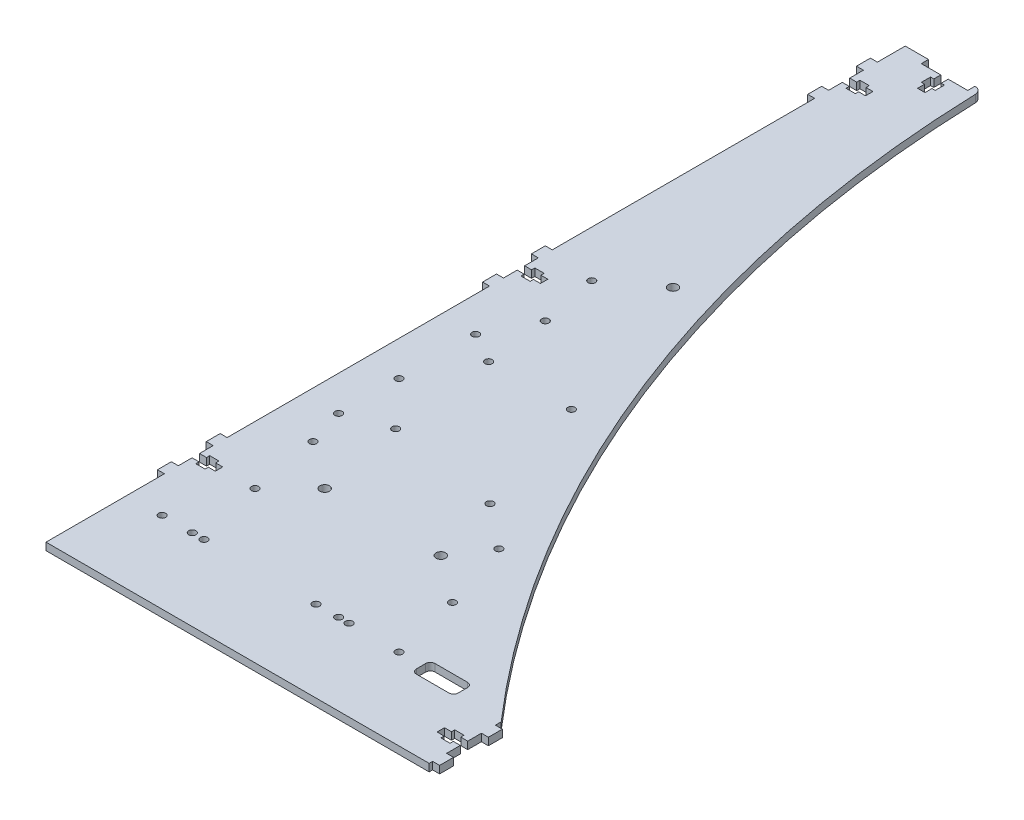
SolidWorks part; units mm, degrees
ref_plane "Alzado" through (0, 0, 0) normal (0, 0, 1) x (1, 0, 0)
ref_plane "Planta" through (0, 0, 0) normal (0, 1, 0) x (1, 0, 0)
ref_plane "Vista lateral" through (0, 0, 0) normal (1, 0, 0) x (0, 0, -1)
sketch "Croquis1" plane through (0, 0, 0) normal (0, 1, 0) x (1, 0, 0)
  line L0 (7, 66.1) -> (10, 66.1)
  line L1 (0, 0) -> (165, 0)
  line L2 (0, 0) -> (0, 51)
  line L3 (0, 370) -> (10, 370)
  line L4 (165, 0) -> (165, 1.5)
  line L5 (0, 51) -> (-3, 51)
  line L7 (0, 57) -> (-3, 57)
  line L8 (-3, 51) -> (-3, 57)
  line L9 (0, 72) -> (-3, 72)
  line L11 (0, 78) -> (-3, 78)
  line L12 (-3, 72) -> (-3, 78)
  line L13 (0, 66.1) -> (3, 66.1)
  line L15 (0, 62.9) -> (3, 62.9)
  line L16 (10, 66.1) -> (10, 62.9)
  line L17 (7, 67.5) -> (3, 67.5)
  line L18 (7, 67.5) -> (7, 66.1)
  line L19 (7, 61.5) -> (3, 61.5)
  line L20 (3, 67.5) -> (3, 66.1)
  line L21 (3, 62.9) -> (3, 61.5)
  line L22 (7, 62.9) -> (7, 61.5)
  line L23 (7, 62.9) -> (10, 62.9)
  line L24 (0, 66.1) -> (0, 72)
  line L25 (0, 78) -> (0, 191)
  line L26 (0, 57) -> (0, 62.9)
  line L27 (0, 218) -> (-3, 218)
  line L28 (-3, 212) -> (-3, 218)
  line L29 (0, 212) -> (-3, 212)
  line L30 (0, 206.1) -> (3, 206.1)
  line L31 (3, 207.5) -> (3, 206.1)
  line L32 (7, 207.5) -> (3, 207.5)
  line L33 (7, 207.5) -> (7, 206.1)
  line L34 (7, 206.1) -> (10, 206.1)
  line L35 (10, 206.1) -> (10, 202.9)
  line L36 (7, 202.9) -> (10, 202.9)
  line L37 (7, 202.9) -> (7, 201.5)
  line L38 (7, 201.5) -> (3, 201.5)
  line L39 (3, 202.9) -> (3, 201.5)
  line L40 (0, 202.9) -> (3, 202.9)
  line L41 (0, 197) -> (-3, 197)
  line L42 (-3, 191) -> (-3, 197)
  line L43 (0, 191) -> (-3, 191)
  line L44 (0, 358) -> (-3, 358)
  line L45 (-3, 352) -> (-3, 358)
  line L46 (0, 352) -> (-3, 352)
  line L47 (0, 346.1) -> (3, 346.1)
  line L48 (3, 347.5) -> (3, 346.1)
  line L49 (7, 347.5) -> (3, 347.5)
  line L50 (7, 347.5) -> (7, 346.1)
  line L51 (7, 346.1) -> (10, 346.1)
  line L52 (10, 346.1) -> (10, 342.9)
  line L53 (7, 342.9) -> (10, 342.9)
  line L54 (7, 342.9) -> (7, 341.5)
  line L55 (7, 341.5) -> (3, 341.5)
  line L56 (3, 342.9) -> (3, 341.5)
  line L57 (0, 342.9) -> (3, 342.9)
  line L58 (0, 337) -> (-3, 337)
  line L59 (-3, 331) -> (-3, 337)
  line L60 (0, 331) -> (-3, 331)
  line L61 (0, 358) -> (0, 370)
  line L62 (0, 346.1) -> (0, 352)
  line L63 (0, 337) -> (0, 342.9)
  line L64 (0, 218) -> (0, 331)
  line L65 (0, 206.1) -> (0, 212)
  line L66 (0, 197) -> (0, 202.9)
  line L67 (21.6, 366.9) -> (30, 366.9)
  line L69 (10, 370) -> (10, 366.9)
  line L70 (10, 366.9) -> (18.4, 366.9)
  line L71 (30, 370) -> (30, 366.9)
  line L73 (18.4, 366.9) -> (18.4, 363.9)
  line L74 (18.4, 356.9) -> (21.6, 356.9)
  line L75 (21.6, 366.9) -> (21.6, 363.9)
  line L76 (17, 363.9) -> (18.4, 363.9)
  line L77 (17, 363.9) -> (17, 359.9)
  line L78 (17, 359.9) -> (18.4, 359.9)
  line L79 (23, 363.9) -> (23, 359.9)
  line L80 (21.6, 363.9) -> (23, 363.9)
  line L81 (18.4, 359.9) -> (18.4, 356.9)
  line L82 (21.6, 359.9) -> (21.6, 356.9)
  line L83 (21.6, 359.9) -> (23, 359.9)
  line L84 (30, 370) -> (165, 370)
  line L85 (158, 13.4) -> (158, 12)
  line L86 (165, 1.5) -> (168, 1.5)
  line L88 (165, 7.5) -> (168, 7.5)
  line L89 (168, 1.5) -> (168, 7.5)
  line L90 (165, 22.5) -> (168, 22.5)
  line L92 (165, 28.5) -> (168, 28.5)
  line L93 (168, 22.5) -> (168, 28.5)
  line L94 (165, 16.6) -> (162, 16.6)
  line L96 (165, 13.4) -> (162, 13.4)
  line L97 (155, 16.6) -> (155, 13.4)
  line L98 (158, 18) -> (162, 18)
  line L99 (158, 18) -> (158, 16.6)
  line L100 (158, 12) -> (162, 12)
  line L101 (162, 18) -> (162, 16.6)
  line L102 (158, 16.6) -> (155, 16.6)
  line L103 (162, 13.4) -> (162, 12)
  line L104 (158, 13.4) -> (155, 13.4)
  line L105 (165, 16.6) -> (165, 22.5)
  line L106 (165, 7.5) -> (165, 13.4)
  line L107 (165, 28.5) -> (165, 370)
  dimension "D1" = 370
  dimension "D2" = 165
  dimension "D3" = 3
  dimension "D4" = 6
  dimension "D5" = 3
  dimension "D6" = 6
  dimension "D7" = 15
  dimension "D8" = 10
  dimension "D9" = 3.2
  dimension "D10" = 5.9
  dimension "D11" = 4
  dimension "D12" = 6
  dimension "D13" = 1.4
  dimension "D14" = 51
  dimension "D15" = 3
  dimension "D17" = 140
  dimension "D18" = 20
  dimension "D19" = 10
  dimension "D20" = 3.1
  dimension "D21" = 10
  dimension "D22" = 3.2
  dimension "D23" = 4
  dimension "D24" = 6
  dimension "D25" = 1.4
  dimension "D26" = 8.4
  dimension "D27" = 3
  dimension "D28" = 6
  dimension "D29" = 6
  dimension "D30" = 3
  dimension "D31" = 3
  dimension "D32" = 3.2
  dimension "D33" = 4
  dimension "D34" = 6
  dimension "D35" = 1.4
  dimension "D36" = 10
  dimension "D37" = 3
  dimension "D38" = 15
  dimension "D39" = 5.9
  dimension "D40" = 1.5
  dimension "D16" = 3
extrude "Saliente-Extruir1" add sketch "Croquis1" along normal blind 3.2
sketch "Croquis2" plane through (0, 0, 0) normal (0, -1, 0) x (1, 0, 0)
  line L0 (30, -370) -> (30, -366.9) construction
  line L1 (165, -370) -> (33, -370)
  line L2 (165, -370) -> (165, -31)
  line L3 (165, -31) -> (33, -31) construction
  line L4 (33, -370) -> (33, -31) construction
  line L5 (168, -28.5) -> (165, -28.5) construction
  arc A0 (33, -370) -> (165, -31) centre (571.6536, -384.5421) cw
  dimension "D1" = 3
  dimension "D2" = 2.5
extrude "Cortar-Extruir1" cut sketch "Croquis2" against normal up to surface (3.2 mm away) up to face at (40.46, 3.2, -191.266)
fillet "Redondeo1" radius 3 1 edges at (33, 1.6, -370)
sketch "Croquis3" plane through (0, 3.2, 0) normal (0, 1, 0) x (1, 0, 0)
  line L0 (0, 202.9) -> (0, 197) construction
  line L1 (0, 0) -> (165, 0) construction
  line L3 (0, 191) -> (0, 78) construction
  line L4 (0, 331) -> (0, 218) construction
  circle A0 centre (40, 80) radius 2.05
  circle A1 centre (90, 80) radius 2.05
  circle A2 centre (40, 230) radius 2.05
  circle A3 centre (20, 95) radius 1.55
  circle A4 centre (20, 215) radius 1.55
  circle A5 centre (100, 95) radius 1.55
  circle A6 centre (25, 65) radius 1.55
  circle A7 centre (25, 190) radius 1.55
  circle A8 centre (110, 65) radius 1.55
  dimension "D1" = 4.1
  dimension "D6" = 3.1
  dimension "D11" = 3.1
  dimension "D2" = 50
  dimension "D3" = 150
  dimension "D4" = 40
  dimension "D5" = 80
  dimension "D7" = 120
  dimension "D8" = 80
  dimension "D9" = 20
  dimension "D10" = 95
  dimension "D12" = 125
  dimension "D13" = 85
  dimension "D14" = 65
  dimension "D15" = 25
extrude "Cortar-Extruir2" cut sketch "Croquis3" against normal up to surface (3.2 mm away) up to face at (40.0076, 0, -191.313)
sketch "Croquis4" plane through (0, 0, 0) normal (0, -1, 0) x (1, 0, 0)
  line L0 (0, -191) -> (0, -78) construction
  line L1 (0, 0) -> (165, 0) construction
  line L2 (0, -51) -> (0, 0) construction
  line L3 (15, -35) -> (15, -111) construction
  line L4 (143, -30.5) -> (129, -30.5)
  line L5 (145, -32.5) -> (145, -36.5)
  line L6 (143, -38.5) -> (129, -38.5)
  line L7 (127, -32.5) -> (127, -36.5)
  circle A0 centre (15, -35) radius 1.55
  circle A1 centre (91, -35) radius 1.55
  circle A2 centre (15, -137) radius 1.55
  circle A4 centre (15, -170) radius 1.55
  circle A5 centre (33, -35) radius 1.55
  circle A6 centre (81.26, -35) radius 1.55
  circle A7 centre (33, -117.55) radius 1.55
  circle A8 centre (81.26, -109.93) radius 1.55
  circle A9 centre (28, -35) radius 1.55
  circle A10 centre (95.48, -35) radius 1.55
  circle A11 centre (28, -162.61) radius 1.55
  circle A12 centre (63.61, -162.61) radius 1.55
  circle A13 centre (117, -35) radius 1.55
  arc A14 (143, -30.5) -> (145, -32.5) centre (143, -32.5) cw
  arc A15 (127, -36.5) -> (129, -38.5) centre (129, -36.5) ccw
  arc A16 (127, -32.5) -> (129, -30.5) centre (129, -32.5) cw
  arc A17 (145, -36.5) -> (143, -38.5) centre (143, -36.5) cw
  circle A18 centre (15, -111) radius 1.55
  point P38 (145, -30.5)
  point P41 (127, -38.5)
  point P46 (145, -38.5)
  dimension "D1" = 76
  dimension "D2" = 102
  dimension "D3" = 3.1
  dimension "D6" = 135
  dimension "D9" = 82.55
  dimension "D10" = 74.93
  dimension "D12" = 28
  dimension "D14" = 35.61
  dimension "D20" = 2
  dimension "D21" = 3.1
  dimension "D4" = 15
  dimension "D5" = 35
  dimension "D7" = 48.26
  dimension "D8" = 33
  dimension "D11" = 67.48
  dimension "D13" = 127.61
  dimension "D15" = 102
  dimension "D16" = 18
  dimension "D17" = 8
  dimension "D18" = 10
  dimension "D19" = 30.5
  dimension "D22" = 76
extrude "Cortar-Extruir3" cut sketch "Croquis4" against normal up to surface (3.2 mm away) up to face at (100, 3.2, -93.45)
